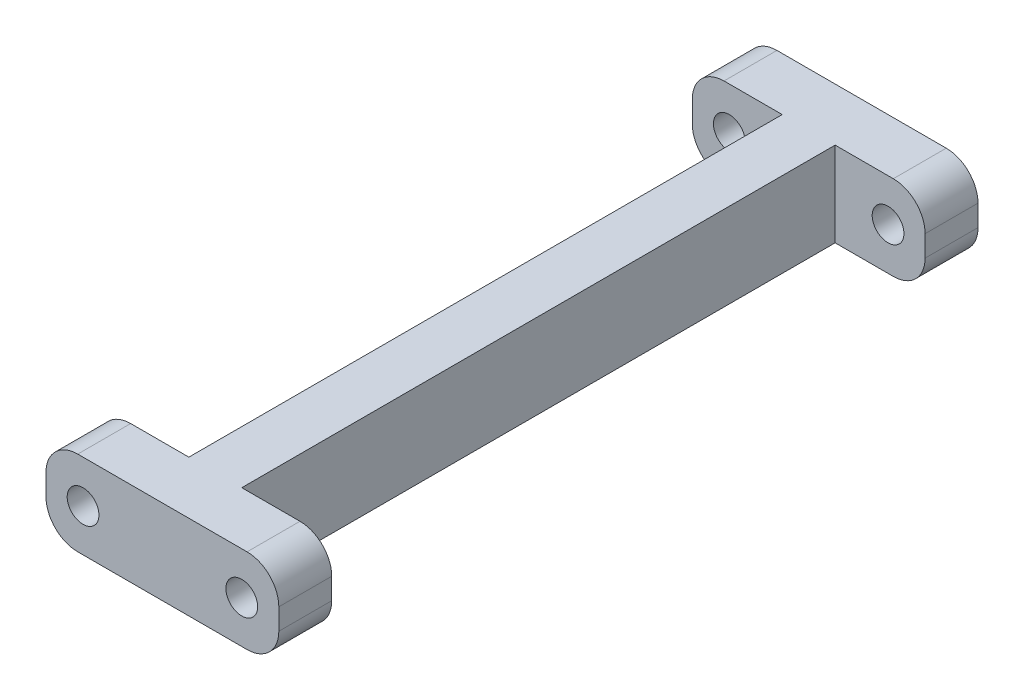
SolidWorks part; units mm, degrees
ref_plane "Front Plane" through (0, 0, 0) normal (0, 0, 1) x (1, 0, 0)
ref_plane "Top Plane" through (0, 0, 0) normal (0, 1, 0) x (1, 0, 0)
ref_plane "Right Plane" through (0, 0, 0) normal (1, 0, 0) x (0, 0, -1)
sketch "Sketch1" plane through (0, 0, 0) normal (0, 0, 1) x (1, 0, 0)
  line L0 (0, 0) -> (3.5, 4) construction
  line L1 (0, 0) -> (22, 0)
  line L2 (0, 0) -> (0, 8)
  line L3 (0, 8) -> (22, 8)
  line L4 (22, 0) -> (22, 8)
  line L5 (3.5, 4) -> (18.5, 4) construction
  line L6 (18.5, 4) -> (22, 0) construction
  line L7 (0, 8) -> (3.5, 4) construction
  line L8 (18.5, 4) -> (22, 8) construction
  circle A0 centre (3.5, 4) radius 1.5
  circle A1 centre (18.5, 4) radius 1.5
  dimension "D1" = 3
  dimension "D2" = 8
  dimension "D3" = 22
  dimension "D4" = 15
extrude "Boss-Extrude1" add sketch "Sketch1" along normal blind 5
sketch "Sketch2" plane through (0, 0, 5) normal (0, 0, 1) x (1, 0, 0)
  line L0 (22, 8) -> (0, 8) construction
  line L1 (8.5, 8) -> (13.5, 8)
  line L2 (8.5, 8) -> (8.5, 0)
  line L3 (8.5, 0) -> (13.5, 0)
  line L4 (13.5, 8) -> (13.5, 0)
  line L5 (0, 0) -> (22, 0) construction
  line L6 (0, 8) -> (8.5, 0) construction
  line L7 (22, 8) -> (13.5, 0) construction
  line L8 (8.5, 0) -> (13.5, 8) construction
  line L9 (8.5, 8) -> (13.5, 0) construction
  line L10 (11, 8) -> (11, 0) construction
  dimension "D1" = 5
extrude "Boss-Extrude2" add sketch "Sketch2" along normal blind 61.0706
sketch "Sketch4" plane through (0, 0, 66.0706) normal (0, 0, 1) x (1, 0, 0)
  line L0 (22, 0) -> (22, 8) construction
  line L1 (0, 0) -> (22, 0) construction
  line L2 (0, 0) -> (0, 8) construction
  line L3 (0, 8) -> (22, 8) construction
  line L4 (22, 0) -> (22, 8)
  line L5 (0, 0) -> (22, 0)
  line L6 (0, 0) -> (0, 8)
  line L7 (0, 8) -> (22, 8)
  circle A0 centre (3.5, 4) radius 1.5 construction
  circle A1 centre (18.5, 4) radius 1.5 construction
  circle A2 centre (3.5, 4) radius 1.5
  circle A3 centre (18.5, 4) radius 1.5
extrude "Boss-Extrude3" add sketch "Sketch4" against normal blind 5
fillet "Fillet1" radius 3 8 edges at (0, 0, 2.5) (0, 8, 2.5) (22, 0, 2.5) (22, 8, 2.5) (22, 8, 63.5706) (22, 0, 63.5706) (0, 0, 63.5706) (0, 8, 63.5706)
